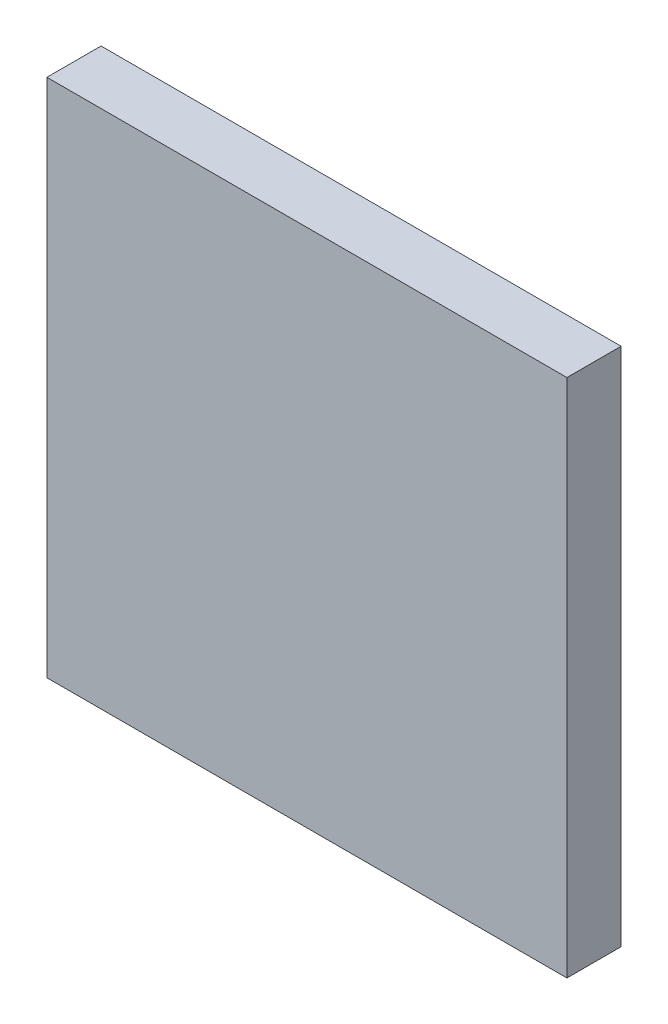
SolidWorks part; units mm, degrees
ref_plane "Front" through (0, 0, 0) normal (0, 0, 1) x (1, 0, 0)
ref_plane "Top" through (0, 0, 0) normal (0, 1, 0) x (1, 0, 0)
ref_plane "Right" through (0, 0, 0) normal (1, 0, 0) x (0, 0, -1)
sketch "Sketch1" plane through (0, 0, 0) normal (0, 0, 1) x (1, 0, 0)
  line L1 (24, -24) -> (-24, -24)
  line L2 (24, -24) -> (24, 24)
  line L3 (24, 24) -> (-24, 24)
  line L4 (-24, -24) -> (-24, 24)
  line L5 (24, -24) -> (-24, 24) construction
  line L6 (24, 24) -> (-24, -24) construction
  point P0 (0, 0)
  point P5 (0, 0)
  dimension "D1" = 48
  dimension "D2" = 48
extrude "Boss-Extrude1" add sketch "Sketch1" along normal blind 5
sketch3d "3DSketch1"
  line L0 (0, 0, 0) -> (0, 0, -50000) construction
  line L1 (24, -24, 0) -> (-24, 24, 0) construction
  point P4 (0, 0, 0)
